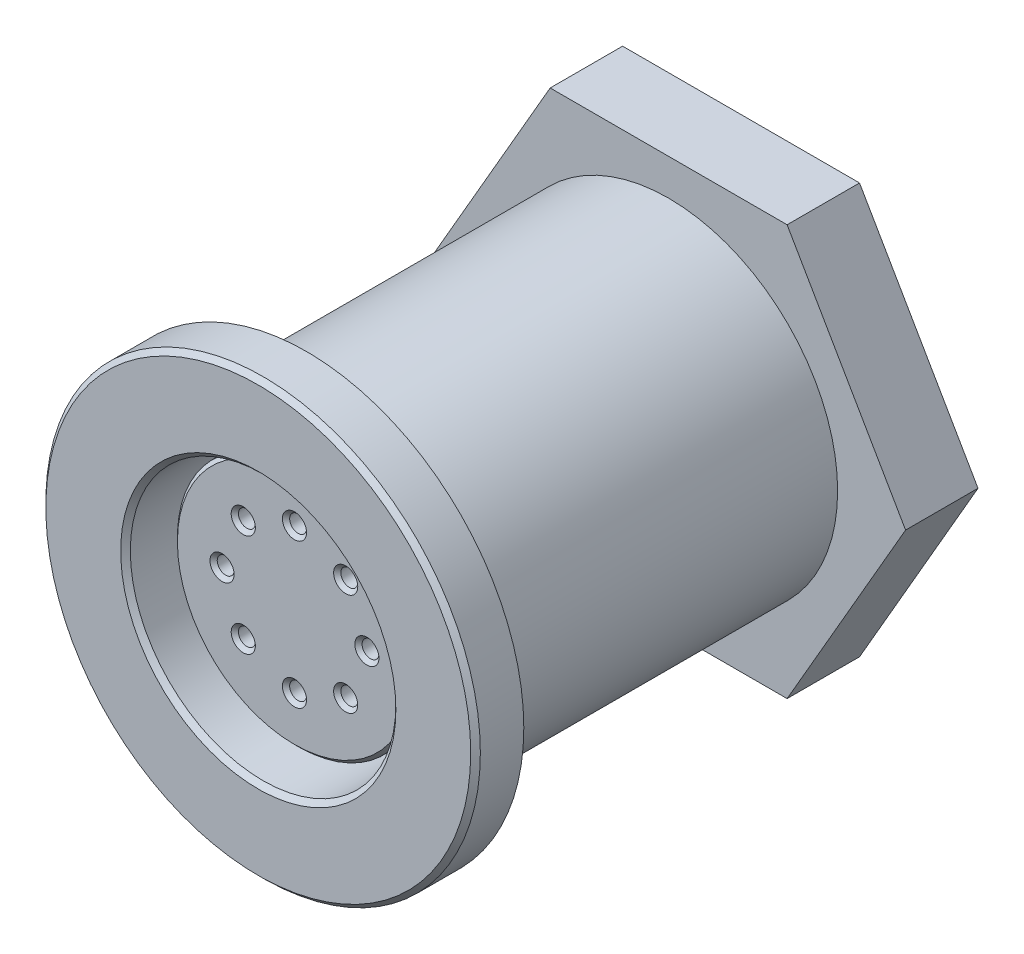
SolidWorks part; units mm, degrees
material "1060 Alloy"
ref_plane "Front Plane" through (0, 0, 0) normal (0, 0, 1) x (1, 0, 0)
ref_plane "Top Plane" through (0, 0, 0) normal (0, 1, 0) x (1, 0, 0)
ref_plane "Right Plane" through (0, 0, 0) normal (1, 0, 0) x (0, 0, -1)
sketch "Sketch1" plane through (0, 0, 0) normal (0, 0, 1) x (1, 0, 0)
  circle A0 centre (0, 0) radius 9
extrude "Extrude1" add sketch "Sketch1" along normal blind 2
sketch "Sketch3" plane through (0, 0, 0) normal (0, 0, -1) x (-1, 0, 0)
  circle A0 centre (0, 0) radius 7.8
  circle A1 centre (0, 0) radius 7
sketch "Sketch4" plane through (0, 0, 0) normal (0, 0, -1) x (-1, 0, 0)
  circle A0 centre (0, 0) radius 7
extrude "Extrude2" add sketch "Sketch4" along normal blind 19
sketch "Sketch2" plane through (0, 0, 2) normal (0, 0, 1) x (1, 0, 0)
  circle A0 centre (0, 0) radius 5.5
extrude "Cut-Extrude1" cut sketch "Sketch2" against normal blind 10
extrude "Cut-Extrude2" cut sketch "Sketch3" against normal blind 1
sketch "Sketch5" plane through (0, 0, -8) normal (0, 0, 1) x (1, 0, 0)
  circle A0 centre (0, 0) radius 5
extrude "Extrude3" add sketch "Sketch5" along normal blind 8.5
sketch "Sketch6" plane through (0, 0, 0.5) normal (0, 0, 1) x (1, 0, 0)
  line L0 (2.1213, 2.1213) -> (0, 0) construction
  line L1 (0, 0) -> (3, 0) construction
  circle A0 centre (0, 3) radius 0.35
  circle A1 centre (0, -3) radius 0.35
  circle A2 centre (2.1213, 2.1213) radius 0.35
  circle A3 centre (2.1213, -2.1213) radius 0.35
  circle A4 centre (-2.1213, 2.1213) radius 0.35
  circle A5 centre (-2.1213, -2.1213) radius 0.35
  circle A6 centre (-3, 0) radius 0.35
  circle A7 centre (3, 0) radius 0.35
  circle A8 centre (0, 0) radius 3 construction
  dimension "D1" = 6
  dimension "D2" = 45
extrude "Cut-Extrude3" cut sketch "Sketch6" against normal blind 7
chamfer "Chamfer2" distance 0.15 angle 45 9 edges at (5, 0, 0.5) (0.35, -3, 0.5) (0.35, 3, 0.5) (2.4713, -2.1213, 0.5) (2.4713, 2.1213, 0.5) (-1.7713, -2.1213, 0.5) (-1.7713, 2.1213, 0.5) (3.35, 0, 0.5) (-2.65, 0, 0.5)
chamfer "Chamfer1" distance 0.2 angle 45 2 edges at (9, 0, 2) (5.5, 0, 2)
sketch "Sketch7" plane through (0, 0, -19) normal (0, 0, -1) x (-1, 0, 0)
  circle A0 centre (0, 0) radius 5
extrude "Cut-Extrude4" cut sketch "Sketch7" against normal blind 1
chamfer "Chamfer3" distance 0.5 angle 45 1 edges at (-7, 0, -19)
sketch "Sketch8" plane through (0, 0, -19) normal (0, 0, -1) x (-1, 0, 0)
  circle A0 centre (0, 0) radius 9
sketch "Sketch9" plane through (0, 0, -18) normal (0, 0, -1) x (-1, 0, 0)
  line L0 (-4.9075, 8.5) -> (4.9075, 8.5)
  line L1 (4.9075, 8.5) -> (9.815, 0)
  line L2 (9.815, 0) -> (4.9075, -8.5)
  line L3 (4.9075, -8.5) -> (-4.9075, -8.5)
  line L4 (-4.9075, -8.5) -> (-9.815, 0)
  line L5 (-9.815, 0) -> (-4.9075, 8.5)
  line L6 (0, 8.5) -> (0, -8.5) construction
  dimension "D1" = 17
  dimension "D2" = 17
extrude "Extrude4" add sketch "Sketch9" against normal blind 3
